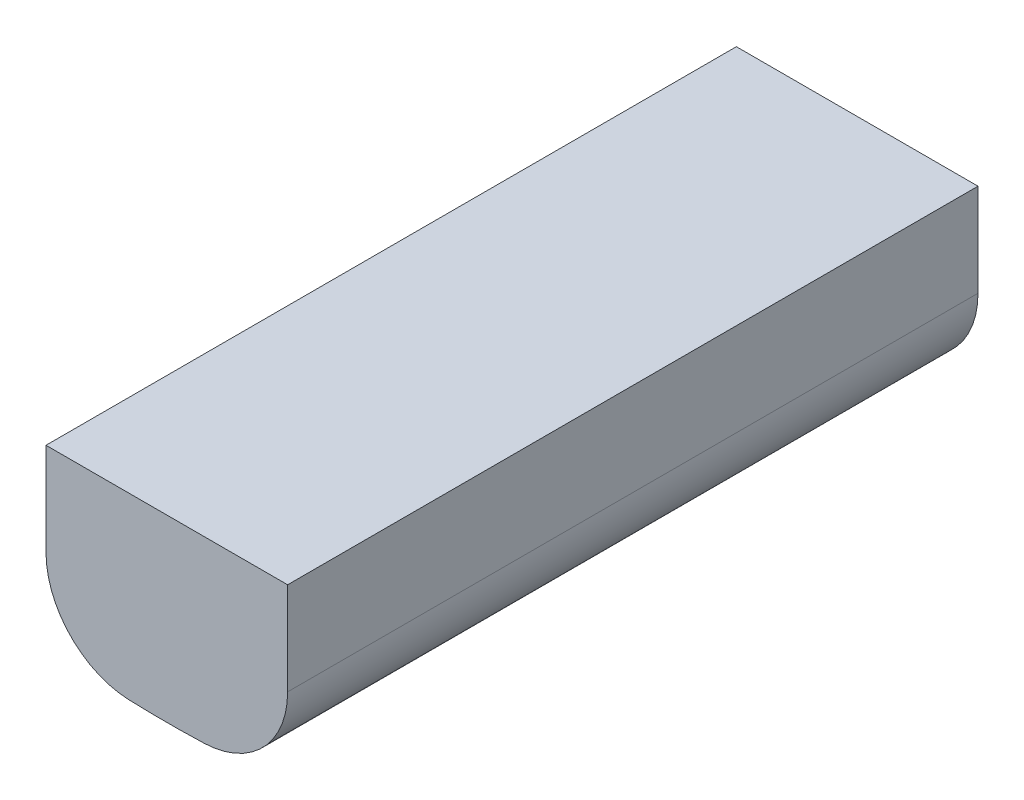
SolidWorks part; units mm, degrees
ref_plane "Alzado" through (0, 0, 0) normal (0, 0, 1) x (1, 0, 0)
ref_plane "Planta" through (0, 0, 0) normal (0, 1, 0) x (1, 0, 0)
ref_plane "Vista lateral" through (0, 0, 0) normal (1, 0, 0) x (0, 0, -1)
sketch "Croquis1" plane through (0, 0, 0) normal (0, 0, 1) x (1, 0, 0)
  line L0 (-0.175, -1.2398) -> (0.175, -1.2398)
  line L1 (0.175, -1.2398) -> (0.175, -1.3741)
  line L2 (-0.175, -1.2398) -> (-0.175, -1.3741)
  arc A0 (-0.0545, -1.499) -> (0.0545, -1.499) centre (0, 0) ccw
  arc A1 (0.175, -1.3741) -> (0.0545, -1.499) centre (0.05, -1.3741) cw
  arc A2 (-0.175, -1.3741) -> (-0.0545, -1.499) centre (-0.05, -1.3741) ccw
  point P4 (0, -1.2398)
  point P8 (0.175, -1.4898)
  dimension "D1" = 3
  dimension "D2" = 0.25
  dimension "D3" = 0.35
  dimension "D4" = 0.125
extrude "Saliente-Extruir1" add sketch "Croquis1" along normal blind 1
